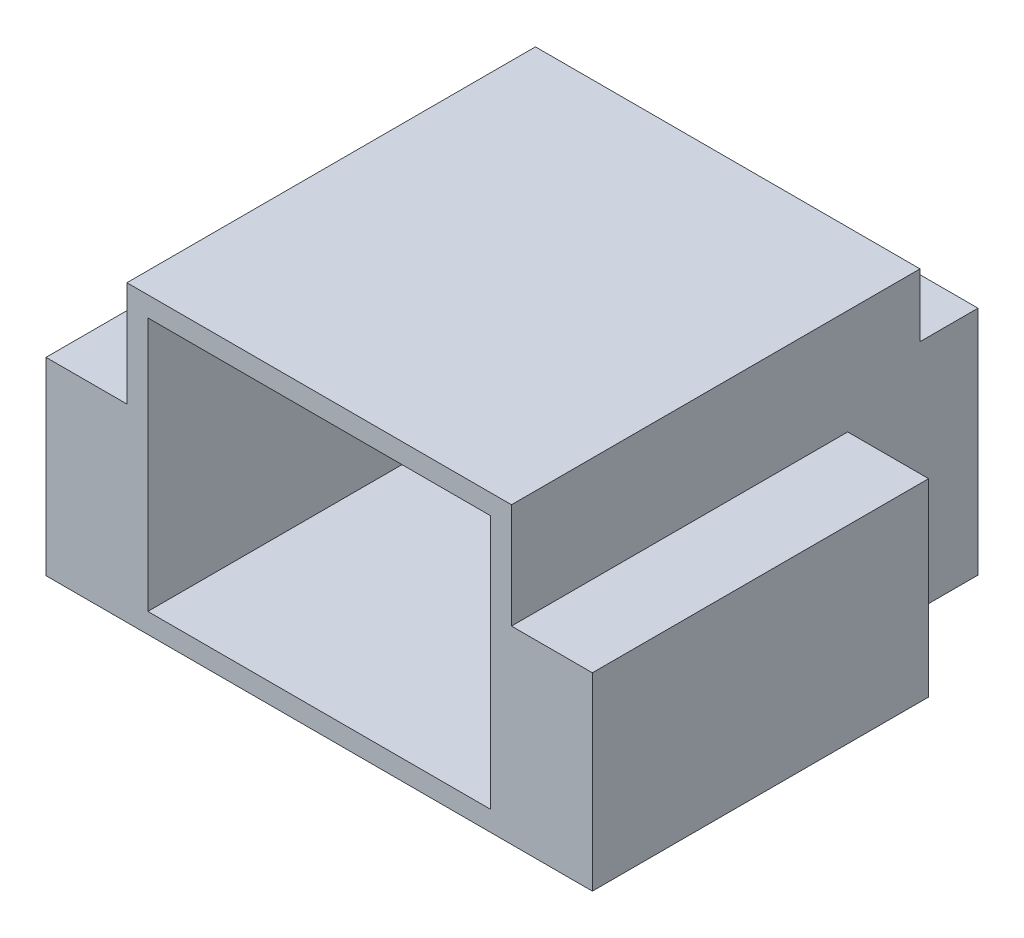
SolidWorks part; units mm, degrees
ref_plane "Front Plane" through (0, 0, 0) normal (0, 0, 1) x (1, 0, 0)
ref_plane "Top Plane" through (0, 0, 0) normal (0, 1, 0) x (1, 0, 0)
ref_plane "Right Plane" through (0, 0, 0) normal (1, 0, 0) x (0, 0, -1)
sketch "Sketch1" plane through (0, 0, 0) normal (0, 1, 0) x (1, 0, 0)
  line L0 (0, 7.1) -> (0, -4) construction
  line L1 (-6.5, -4) -> (6.5, -4)
  line L2 (-6.5, -4) -> (-6.5, 4)
  line L3 (-6.5, 4) -> (6.5, 4)
  line L4 (6.5, -4) -> (6.5, 4)
  line L5 (-6.5, -4) -> (6.5, 4) construction
  line L6 (-6.5, 4) -> (6.5, -4) construction
  line L7 (-4.575, 4) -> (4.575, 4)
  line L8 (-4.575, 4) -> (-4.575, 7.1)
  line L9 (-4.575, 7.1) -> (4.575, 7.1)
  line L10 (4.575, 4) -> (4.575, 7.1)
  point P0 (0, 0)
  dimension "D1" = 11.1
  dimension "D2" = 13
  dimension "D3" = 9.15
  dimension "D4" = 8
extrude "Boss-Extrude1" add sketch "Sketch1" along normal blind 7 contours L3 L10 L9 L8 | L1 L4 L3 L2
sketch "Sketch2" plane through (0, 7, 0) normal (0, 1, 0) x (1, 0, 0)
  line L1 (-4.575, 4) -> (-6.5, 4)
  line L2 (-4.575, 4) -> (-4.575, -4)
  line L3 (-4.575, -4) -> (-6.5, -4)
  line L4 (-6.5, 4) -> (-6.5, -4)
  line L5 (4.575, 4) -> (6.5, 4)
  line L6 (4.575, 4) -> (4.575, -4)
  line L7 (4.575, -4) -> (6.5, -4)
  line L8 (6.5, 4) -> (6.5, -4)
extrude "Cut-Extrude1" cut sketch "Sketch2" against normal blind 2.5
sketch "Sketch3" plane through (0, 7, 0) normal (0, 1, 0) x (1, 0, 0)
  line L0 (4.575, -4) -> (4.575, 7.1) construction
  line L1 (-4.575, 7.1) -> (4.575, 7.1)
  line L2 (-4.575, 7.1) -> (-4.575, 5.7206)
  line L3 (-4.575, 5.7206) -> (4.575, 5.7206)
  line L4 (4.575, 7.1) -> (4.575, 5.7206)
extrude "Cut-Extrude2" cut sketch "Sketch3" against normal blind 1.5
sketch "Sketch4" plane through (0, 0, 4) normal (0, 0, 1) x (1, 0, 0)
  line L0 (-4.575, 7) -> (-4.575, 0)
  line L1 (-6.5, 0) -> (6.5, 0) construction
  line L2 (4.575, 7) -> (4.575, 0)
  line L3 (-4.575, 7) -> (4.575, 7) construction
  line L4 (4.575, 4.5) -> (4.575, 7) construction
  line L5 (-4.575, 3.5) -> (4.575, 3.5) construction
  line L6 (0, 7) -> (0, 0) construction
  line L8 (-4.0776, 0.4756) -> (4.0776, 0.4756)
  line L9 (-4.0776, 0.4756) -> (-4.0776, 6.5244)
  line L10 (-4.0776, 6.5244) -> (4.0776, 6.5244)
  line L11 (4.0776, 0.4756) -> (4.0776, 6.5244)
  line L12 (-4.0776, 0.4756) -> (4.0776, 6.5244) construction
  line L13 (-4.0776, 6.5244) -> (4.0776, 0.4756) construction
  point P14 (0, 3.5)
extrude "Cut-Extrude3" cut sketch "Sketch4" against normal blind 8 contours L8 L11 L10 L9
